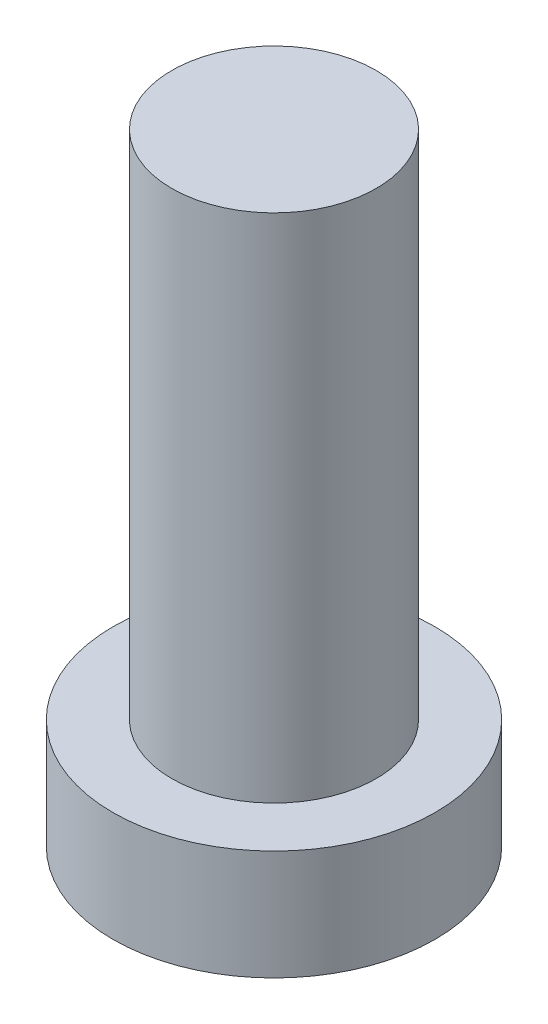
SolidWorks part; units mm, degrees
ref_plane "前视基准面" through (0, 0, 0) normal (0, 0, 1) x (1, 0, 0)
ref_plane "上视基准面" through (0, 0, 0) normal (0, 1, 0) x (1, 0, 0)
ref_plane "右视基准面" through (0, 0, 0) normal (1, 0, 0) x (0, 0, -1)
sketch "草图1" plane through (0, 0, 0) normal (0, 1, 0) x (1, 0, 0)
  circle A0 centre (0, 0) radius 3.15
extrude "凸台-拉伸1" add sketch "草图1" along normal blind 2.15
sketch "草图2" plane through (0, 2.15, 0) normal (0, 1, 0) x (1, 0, 0)
  circle A0 centre (0, 0) radius 2
extrude "凸台-拉伸2" add sketch "草图2" along normal blind 10
sketch "草图3" plane through (0, 0, 0) normal (0, -1, 0) x (1, 0, 0)
  line L0 (-0.5, 1) -> (-0.5, 2)
  line L1 (-2, -0.5) -> (-1, -0.5)
  line L2 (-2, -0.5) -> (-2, 0.5)
  line L3 (-2, 0.5) -> (-1, 0.5)
  line L4 (2, -0.5) -> (2, 0.5)
  line L5 (-2, -0.5) -> (2, 0.5) construction
  line L6 (-2, 0.5) -> (2, -0.5) construction
  line L7 (-0.5, -2) -> (0.5, -2)
  line L8 (-0.5, -2) -> (-0.5, -1)
  line L9 (-0.5, 2) -> (0.5, 2)
  line L10 (0.5, -2) -> (0.5, -1)
  line L11 (-0.5, -2) -> (0.5, 2) construction
  line L12 (-0.5, 2) -> (0.5, -2) construction
  line L13 (1, -0.5) -> (2, -0.5)
  line L14 (0.5, 1) -> (0.5, 2)
  line L15 (1, 0.5) -> (2, 0.5)
  arc A0 (-0.5, -1) -> (-1, -0.5) centre (-1, -1) ccw
  arc A1 (1, -0.5) -> (0.5, -1) centre (1, -1) ccw
  arc A2 (0.5, 1) -> (1, 0.5) centre (1, 1) ccw
  arc A3 (-0.5, 1) -> (-1, 0.5) centre (-1, 1) cw
  point P0 (0, 0)
  point P6 (0, 0)
  point P21 (0.5, 0.5)
  dimension "D1" = 0.5
extrude "切除-拉伸1" cut sketch "草图3" against normal blind 1.5
